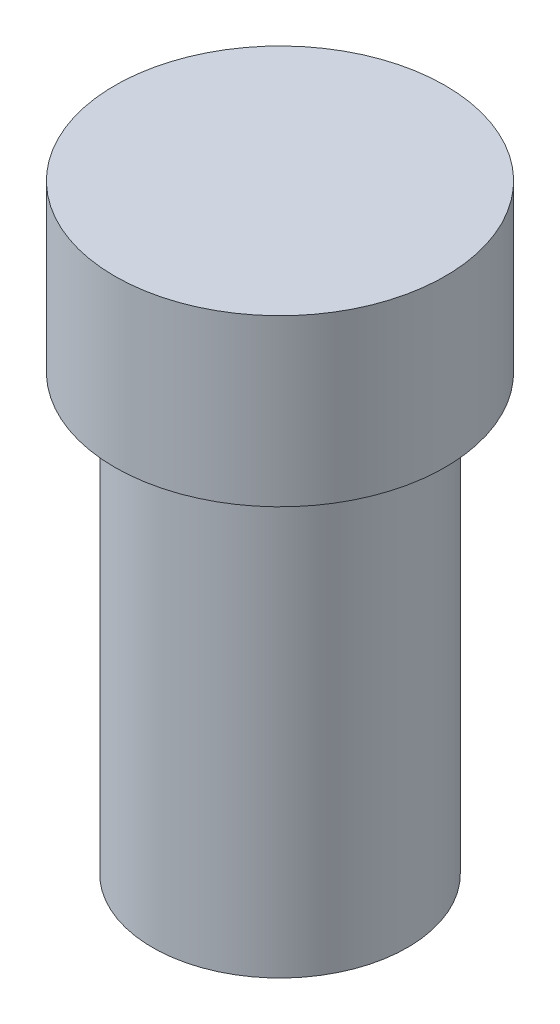
SolidWorks part; units mm, degrees
ref_plane "Front Plane" through (0, 0, 0) normal (0, 0, 1) x (1, 0, 0)
ref_plane "Top Plane" through (0, 0, 0) normal (0, 1, 0) x (1, 0, 0)
ref_plane "Right Plane" through (0, 0, 0) normal (1, 0, 0) x (0, 0, -1)
sketch "Sketch1" plane through (0, 0, 0) normal (0, 0, 1) x (1, 0, 0)
  line L0 (0, 0) -> (0, 50000) construction
  line L1 (-1044, 0) -> (-22, 0) construction
  line L2 (0, 0) -> (50000, 0) construction
  line L3 (0, -75) -> (-22, -75)
  line L4 (0, -75) -> (0, 0)
  line L6 (-22, -75) -> (-22, 0)
  line L7 (-22, 0) -> (-28.5, 0)
  line L8 (0, 0) -> (0, 28.5509)
  line L9 (0, 28.5509) -> (-28.5, 28.5509)
  line L10 (-28.5, 0) -> (-28.5, 28.5509)
  dimension "D1" = 22
  dimension "D2" = 75
  dimension "D3" = 28.5
revolve "Revolve1" add sketch "Sketch1" angle 360 about L0
